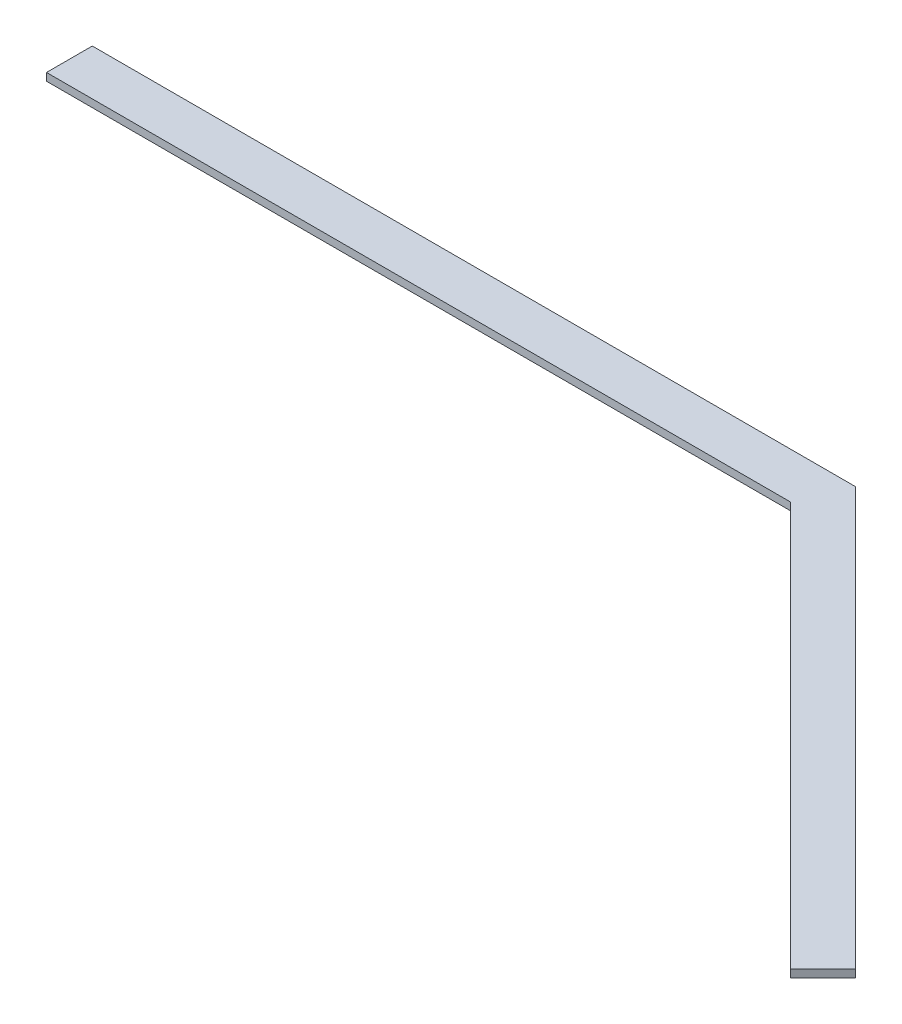
SolidWorks part; units mm, degrees
ref_plane "Front Plane" through (0, 0, 0) normal (0, 0, 1) x (1, 0, 0)
ref_plane "Top Plane" through (0, 0, 0) normal (0, 1, 0) x (1, 0, 0)
ref_plane "Right Plane" through (0, 0, 0) normal (1, 0, 0) x (0, 0, -1)
sketch "Sketch1" plane through (0, 0, 0) normal (0, 1, 0) x (1, 0, 0)
  line L1 (-273.7868, 273.7868) -> (-773.7868, 273.7868)
  line L2 (-773.7868, 273.7868) -> (-773.7868, 243.7868)
  line L3 (-773.7868, 243.7868) -> (-286.2132, 243.7868)
  line L4 (-286.2132, 243.7868) -> (-21.2132, -21.2132)
  line L6 (-273.7868, 273.7868) -> (0, 0)
  line L13 (-21.2132, -21.2132) -> (0, 0)
  dimension "D1" = 30
  dimension "D2" = 30
  dimension "D3" = 500
  dimension "D4" = 90
  dimension "D5" = 135
  dimension "D6" = 265
extrude "Boss-Extrude1" add sketch "Sketch1" along normal blind 5
